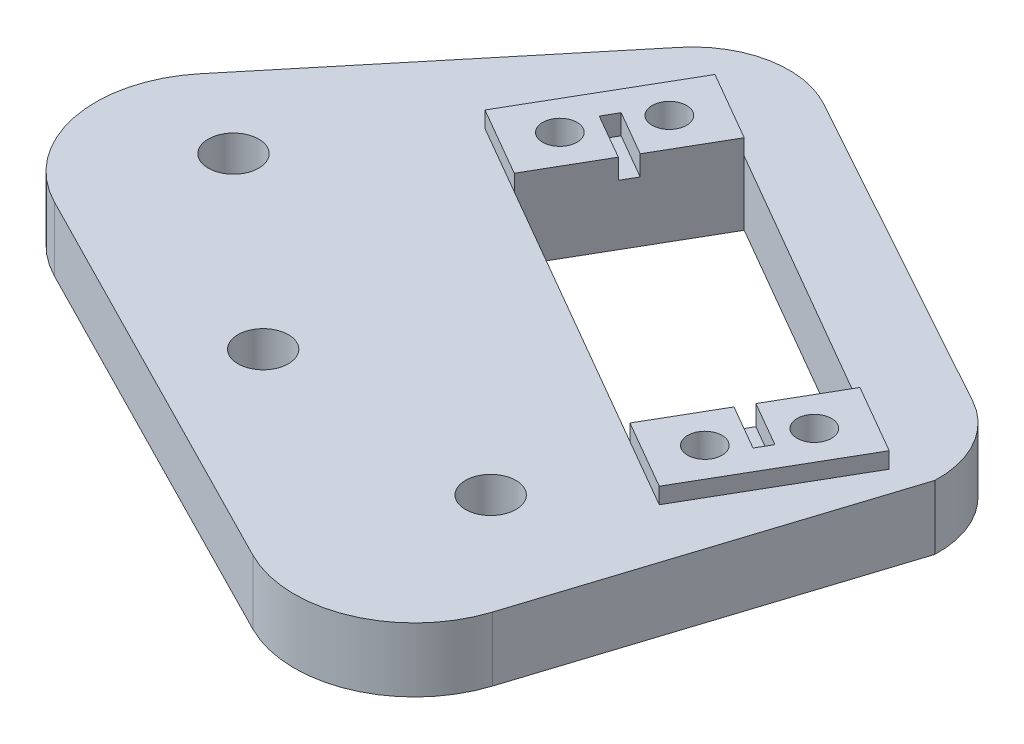
SolidWorks part; units mm, degrees
ref_plane "Front Plane" through (0, 0, 0) normal (0, 0, 1) x (1, 0, 0)
ref_plane "Top Plane" through (0, 0, 0) normal (0, 1, 0) x (1, 0, 0)
ref_plane "Right Plane" through (0, 0, 0) normal (1, 0, 0) x (0, 0, -1)
sketch "Sketch1" plane through (0, 0, 0) normal (0, 1, 0) x (1, 0, 0)
  line L9 (-36.0642, 30.1982) -> (-36.0642, 45.0551)
  line L11 (5.0242, -12.5754) -> (57.86, 4.654)
  line L13 (57.86, 4.654) -> (63.1927, 49.9788)
  line L14 (63.1927, 49.9788) -> (25.9283, 75.0284)
  line L15 (25.9283, 75.0284) -> (-24.4562, 60.5082)
  line L18 (-26.7937, -0.9344) -> (-36.0642, 30.1982)
  line L19 (-36.0642, 45.0551) -> (-24.4562, 60.5082)
  line L23 (5.0242, -12.5754) -> (-26.7937, -0.9344)
extrude "Boss-Extrude2" add sketch "Sketch1" along normal blind 8
sketch "Sketch2" plane through (0, 8, 0) normal (0, 1, 0) x (1, 0, 0)
  line L0 (-0.9926, 5.0237) -> (-23.9739, 24.3073)
  circle A0 centre (-0.9926, 5.0237) radius 3.15
  circle A1 centre (-23.9739, 24.3073) radius 3.15
extrude "Cut-Extrude1" cut sketch "Sketch2" against normal blind 8
sketch "Sketch3" plane through (0, 8, 0) normal (0, 1, 0) x (1, 0, 0)
  line L0 (45.7659, 22.0197) -> (-5.7479, 51.7951)
  line L1 (-5.7479, 51.7951) -> (-0.4934, 60.8858)
  line L2 (-0.4934, 60.8858) -> (8.1644, 55.8815)
  line L3 (8.1644, 55.8815) -> (-2.3446, 37.7002)
  line L4 (-2.3446, 37.7002) -> (-11.0024, 42.7044)
  line L5 (-11.0024, 42.7044) -> (-5.7479, 51.7951)
  line L8 (45.7659, 22.0197) -> (51.0204, 31.1104)
  line L9 (51.0204, 31.1104) -> (42.3626, 36.1146)
  line L10 (42.3626, 36.1146) -> (31.8536, 17.9333)
  line L11 (31.8536, 17.9333) -> (40.5114, 12.929)
  line L12 (40.5114, 12.929) -> (45.7659, 22.0197)
extrude "Boss-Extrude4" add sketch "Sketch3" along normal blind 2 contours L3 L2 L1 L0 | L5 L4 L3 L0 | L9 L10 L0 L8 | L11 L12 L0 L10
sketch "Sketch4" plane through (0, 8, 0) normal (0, 1, 0) x (1, 0, 0)
  line L0 (8.1644, 55.8815) -> (-2.3446, 37.7002)
  line L1 (-2.3446, 37.7002) -> (31.8536, 17.9333)
  line L2 (31.8536, 17.9333) -> (42.3626, 36.1146)
  line L3 (42.3626, 36.1146) -> (8.1644, 55.8815)
extrude "Cut-Extrude2" cut sketch "Sketch4" against normal blind 14
sketch "Sketch5" plane through (0, 10, 0) normal (0, 1, 0) x (1, 0, 0)
  line L0 (2.9099, 46.7908) -> (-1.419, 49.293)
  line L1 (8.1644, 55.8815) -> (-2.3446, 37.7002) construction
  line L2 (-1.419, 49.293) -> (-3.9212, 44.9641)
  line L3 (-1.419, 49.293) -> (1.0831, 53.6219)
  line L4 (37.1081, 27.024) -> (41.437, 24.5218)
  line L5 (42.3626, 36.1146) -> (31.8536, 17.9333) construction
  line L6 (41.437, 24.5218) -> (43.9392, 28.8507)
  line L7 (41.437, 24.5218) -> (38.9349, 20.1929)
  circle A0 centre (-3.9212, 44.9641) radius 2.15
  circle A1 centre (1.0831, 53.6219) radius 2.15
  circle A2 centre (43.9392, 28.8507) radius 2.15
  circle A3 centre (38.9349, 20.1929) radius 2.15
extrude "Cut-Extrude3" cut sketch "Sketch5" against normal blind 14
sketch "Sketch6" plane through (0, 0, 0) normal (0, -1, 0) x (1, 0, 0)
  circle A0 centre (43.9392, -28.8507) radius 3.5
  circle A1 centre (38.9349, -20.1929) radius 3.5
  circle A2 centre (1.0831, -53.6219) radius 3.5
  circle A3 centre (-3.9212, -44.9641) radius 3.5
extrude "Cut-Extrude4" cut sketch "Sketch6" against normal blind 2.6
sketch "Sketch7" plane through (0, 8, 0) normal (0, 1, 0) x (1, 0, 0)
  line L0 (-40.8206, 23.4296) -> (-5.3719, -12.0191)
  line L1 (-40.8206, 23.4296) -> (-8.1976, 82.9275)
  line L2 (-8.1976, 82.9275) -> (73.0578, 41.0836)
  line L3 (73.0578, 41.0836) -> (42.9406, -17.4001)
  line L4 (42.9406, -17.4001) -> (-5.3719, -12.0191)
  line L5 (-23.9008, 101.0328) -> (-57.9014, 20.737)
  line L6 (-57.9014, 20.737) -> (-18.159, -32.5338)
  line L7 (-18.159, -32.5338) -> (87.9242, -9.9612)
  line L8 (87.9242, -9.9612) -> (85.312, 49.3156)
  line L9 (85.312, 49.3156) -> (-23.9008, 101.0328)
extrude "Cut-Extrude5" cut sketch "Sketch7" against normal blind 18.5
sketch "Sketch8" plane through (0, 8, 0) normal (0, 1, 0) x (1, 0, 0)
  line L0 (-8.1976, 82.9275) -> (-40.8206, 23.4296)
  line L1 (-40.8206, 23.4296) -> (-5.3719, -12.0191)
  line L2 (-5.3719, -12.0191) -> (42.9406, -17.4001)
  line L3 (42.9406, -17.4001) -> (73.0578, 41.0836)
  line L4 (73.0578, 41.0836) -> (-8.1976, 82.9275)
  line L5 (7.4196, 62.0055) -> (-9.7469, 64.7472)
  line L6 (13.8825, 71.557) -> (-19.7459, 61.8657) construction
  line L7 (-9.7469, 64.7472) -> (-32.4016, 23.4296)
  line L8 (-32.4016, 23.4296) -> (0, -4.6748)
  line L9 (0, -4.6748) -> (46.1975, 11.8418)
  line L10 (46.1975, 11.8418) -> (56.0255, 35.9436)
  line L11 (56.0255, 35.9436) -> (7.4196, 62.0055)
extrude "Boss-Extrude7" add sketch "Sketch8" against normal blind 8
sketch "Sketch9" plane through (0, 0, 0) normal (0, -1, 0) x (-1, 0, 0)
  circle A0 centre (-28.9418, 3.4739) radius 3.15
extrude "Cut-Extrude6" cut sketch "Sketch9" against normal blind 8
sketch "Sketch10" plane through (0, 8, 0) normal (0, 1, 0) x (1, 0, 0)
  line L0 (-33.8726, 31.8418) -> (-7.6109, 63.6375)
  line L1 (7.4316, 66.5062) -> (48.8705, 43.6771)
  line L3 (42.9406, -17.4001) -> (73.0578, 41.0836) construction
  line L6 (-40.8206, 23.4296) -> (-5.3719, -12.0191) construction
  line L8 (-51.0279, 26.4997) -> (-18.338, 89.9793)
  line L9 (-18.338, 89.9793) -> (70.6189, 64.73)
  line L10 (70.6189, 64.73) -> (85.8622, 8.3294)
  line L11 (85.8622, 8.3294) -> (41.1982, -31.6467)
  line L12 (41.1982, -31.6467) -> (-23.676, -9.8144)
  line L13 (-23.676, -9.8144) -> (-51.0279, 26.4997)
  line L14 (55.073, 32.7548) -> (41.7063, -9.0649)
  line L15 (-33.8726, 31.8418) -> (-34.7005, 30.8395)
  line L16 (-29.9508, 7.925) -> (20.6029, -17.8603)
  arc A2 (55.073, 32.7548) -> (48.8705, 43.6771) centre (43.0801, 33.1665) ccw
  arc A3 (7.4316, 66.5062) -> (-7.6109, 63.6375) centre (1.6412, 55.9956) ccw
  arc A7 (41.7063, -9.0649) -> (20.6029, -17.8603) centre (27.4184, -4.4981) cw
  arc A8 (-29.9508, 7.925) -> (-34.7005, 30.8395) centre (-23.1353, 21.2872) cw
  point P20 (-9.3641, -8.0269)
  point P23 (54.0948, 4.26)
  point P30 (42.9406, -17.4001)
  point P33 (-40.8206, 23.4296)
  dimension "D1" = 15
extrude "Cut-Extrude8" cut sketch "Sketch10" against normal blind 8
sketch "Sketch12" plane through (0, 8, 0) normal (0, 1, 0) x (1, 0, 0)
  line L0 (-34.7005, 30.8395) -> (-23.7994, 10.8786)
  line L1 (-23.7994, 10.8786) -> (16.2733, -10.7751)
  line L2 (16.2733, -10.7751) -> (41.7063, -9.0649)
  line L3 (-29.9508, 7.925) -> (20.6029, -17.8603)
  arc A0 (-34.7005, 30.8395) -> (-29.9508, 7.925) centre (-23.1353, 21.2872) ccw
  arc A1 (20.6029, -17.8603) -> (41.7063, -9.0649) centre (27.4184, -4.4981) ccw
extrude "Boss-Extrude8" add sketch "Sketch12" against normal blind 8
sketch "Sketch13" plane through (0, 10, 0) normal (0, 1, 0) x (1, 0, 0)
  line L0 (37.1081, 27.024) -> (37.6086, 27.8897)
  line L7 (42.3626, 36.1146) -> (31.8536, 17.9333) construction
  line L8 (37.6086, 27.8897) -> (43.2361, 24.637)
  line L9 (43.2361, 24.637) -> (42.2353, 22.9054)
  line L10 (42.2353, 22.9054) -> (36.6077, 26.1582)
  line L11 (36.6077, 26.1582) -> (37.1081, 27.024)
  line L12 (8.1644, 55.8815) -> (-2.3446, 37.7002) construction
  line L13 (3.4103, 47.6566) -> (-2.2173, 50.9094)
  line L14 (-2.2173, 50.9094) -> (-3.2181, 49.1778)
  line L15 (-3.2181, 49.1778) -> (2.4095, 45.9251)
  line L16 (2.4095, 45.9251) -> (3.4103, 47.6566)
extrude "Cut-Extrude9" cut sketch "Sketch13" against normal blind 2.5
